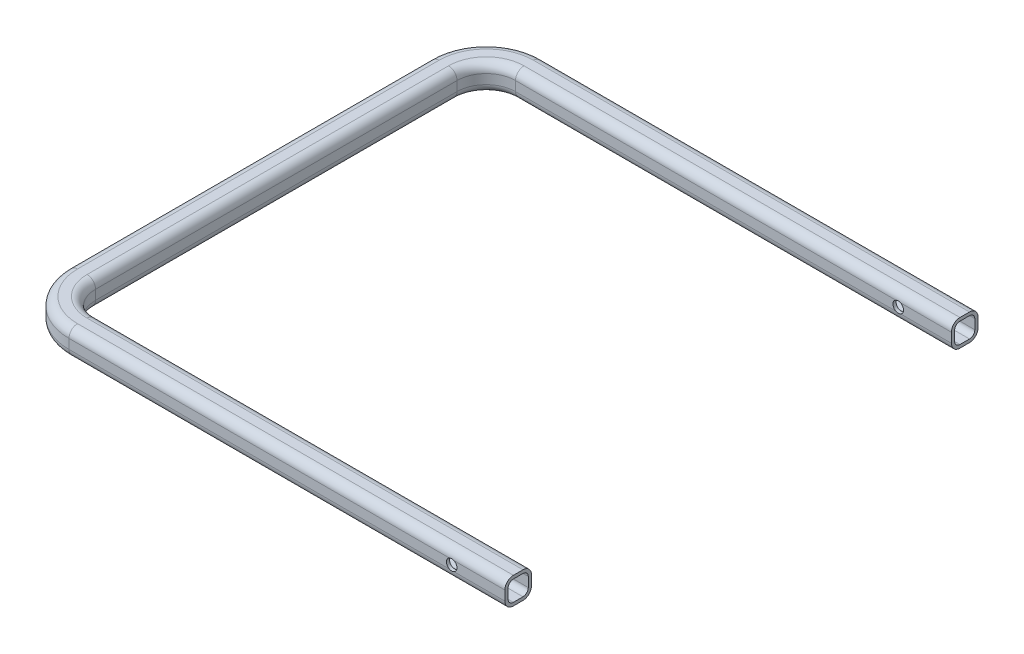
SolidWorks part; units mm, degrees
material "5052-H38, Rod (SS)"
ref_plane "Front Plane" through (0, 0, 0) normal (0, 0, 1) x (1, 0, 0)
ref_plane "Top Plane" through (0, 0, 0) normal (0, 1, 0) x (1, 0, 0)
ref_plane "Right Plane" through (0, 0, 0) normal (1, 0, 0) x (0, 0, -1)
sketch "Sketch1" plane through (0, 0, 0) normal (0, 1, 0) x (1, 0, 0)
  line L0 (0, 0) -> (-410, 0)
  line L1 (-450, 40) -> (-450, 380)
  line L2 (-410, 420) -> (0, 420)
  line L3 (-50, 0) -> (-50, 420) construction
  line L4 (-450, 210) -> (-457.5631, 210) construction
  arc A0 (-410, 0) -> (-450, 40) centre (-410, 40) cw
  arc A1 (-410, 420) -> (-450, 380) centre (-410, 380) ccw
  point P7 (-450, 0)
  point P10 (-450, 420)
  dimension "D3" = 40
  dimension "D1" = 450
  dimension "D2" = 420
  dimension "D4" = 50
sketch "Sketch2" plane through (0, 0, 0) normal (1, 0, 0) x (0, 0, -1)
  line L1 (-4.5, -9.5) -> (4.5, -9.5)
  line L2 (-9.5, -4.5) -> (-9.5, 4.5)
  line L3 (-4.5, 9.5) -> (4.5, 9.5)
  line L4 (9.5, -4.5) -> (9.5, 4.5)
  line L5 (-9.5, -9.5) -> (9.5, 9.5) construction
  line L6 (-9.5, 9.5) -> (9.5, -9.5) construction
  arc A0 (-4.5, 9.5) -> (-9.5, 4.5) centre (-4.5, 4.5) ccw
  arc A1 (-9.5, -4.5) -> (-4.5, -9.5) centre (-4.5, -4.5) ccw
  arc A2 (4.5, -9.5) -> (9.5, -4.5) centre (4.5, -4.5) ccw
  arc A3 (9.5, 4.5) -> (4.5, 9.5) centre (4.5, 4.5) ccw
  point P0 (0, 0)
  dimension "D3" = 5
  dimension "D1" = 19
  dimension "D2" = 19
sweep "Sweep-Thin1" add profiles "Sketch2" path "Sketch1" parameters "D1"=3
sketch "Sketch3" plane through (0, 0, 0) normal (0, 0, 1) x (1, 0, 0)
  line L0 (0, 0) -> (-410, 0) construction
  circle A0 centre (-50, 0) radius 5
  dimension "D1" = 50
extrude "Cut-Extrude1" cut sketch "Sketch3" against normal through all and the other way through all
sketch "Sketch4" plane through (0, 0, -12.5) normal (0, 0, -1) x (-1, 0, 0)
  line L0 (0, 0) -> (45, 0) construction
  line L1 (0, -4.5) -> (0, 4.5) construction
  arc A0 (47.8206, 4.5) -> (47.8206, -4.5) centre (50, 0) ccw construction
ref_plane "Plane1" through (-450, 0, 0) normal (1, 0, 0) x (0, 0, -1)
sketch "Sketch5" plane through (-450, 0, 0) normal (1, 0, 0) x (0, 0, -1)
  line L0 (380, 0) -> (38.7593, 0) construction
  line L1 (209.3797, 0) -> (281.8797, 0) construction
  line L3 (209.3797, 0) -> (136.8797, 0) construction
  line L4 (281.8797, 0) -> (281.8797, -50) construction
  line L5 (136.8797, 0) -> (136.8797, -50) construction
  dimension "D1" = 72.5
  dimension "D2" = 72.5
ref_plane "Plane2" through (0, 0, -210) normal (0, 0, -1) x (-1, 0, 0)
